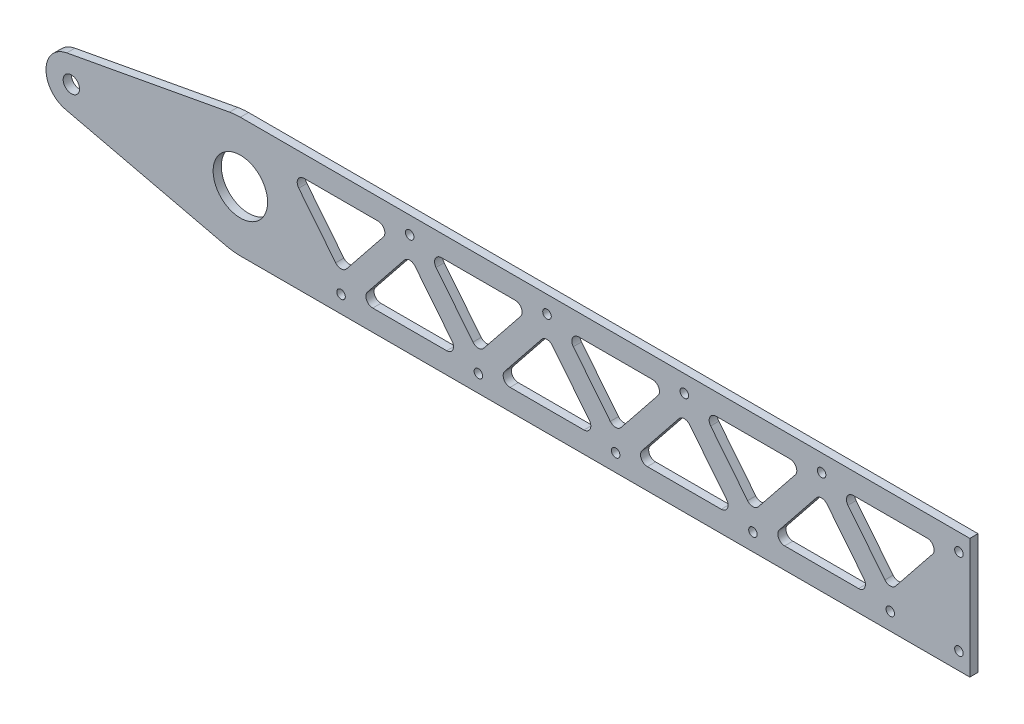
SolidWorks part; units mm, degrees
material "6061-T6 (SS)"
ref_plane "Front" through (0, 0, 0) normal (0, 0, 1) x (1, 0, 0)
ref_plane "Top" through (0, 0, 0) normal (0, 1, 0) x (1, 0, 0)
ref_plane "Right" through (0, 0, 0) normal (1, 0, 0) x (0, 0, -1)
sketch "Sketch1" plane through (0, 0, 0) normal (0, 0, 1) x (1, 0, 0)
  line L0 (-212.5, 35) -> (212.5, 35)
  line L1 (-212.5, -35) -> (212.5, -35)
  line L2 (-212.5, 0) -> (212.5, 0) construction
  line L6 (-212.5, 35) -> (-212.5, -35) construction
  line L8 (212.5, 35) -> (212.5, -35)
  line L9 (-313.6661, 16.8908) -> (-218.8625, 34.4168)
  line L10 (-314.3603, -12.0155) -> (-220.5071, -34.0718)
  arc A0 (-212.5, 35) -> (-218.8625, 34.4168) centre (-212.5, 0) ccw
  circle A2 centre (-212.5, 0) radius 15.875
  circle A4 centre (-310.9808, 2.3648) radius 4.7625
  arc A5 (-313.6661, 16.8908) -> (-314.3603, -12.0155) centre (-310.9808, 2.3648) ccw
  arc A6 (-220.5071, -34.0718) -> (-212.5, -35) centre (-212.5, 0) ccw
  point P6 (0, 0)
  dimension "D2" = 35
  dimension "D3" = 31.75
  dimension "D4" = 98.4808
  dimension "D7" = 9.525
  dimension "D6" = 14.7721
  dimension "D1" = 425
  dimension "D5" = 2.3648
extrude "Boss-Extrude1" add sketch "Sketch1" along normal blind 4.7625
sketch "Sketch6" plane through (0, 0, 0) normal (0, 0, -1) x (-1, 0, 0)
  line L0 (-166.15, 35) -> (-166.15, -35) construction
  line L1 (212.5, 35) -> (-212.5, 35) construction
  line L2 (212.5, -35) -> (-212.5, -35) construction
  line L3 (-212.5, 35) -> (-212.5, -35) construction
  circle A0 centre (212.5, 0) radius 50 construction
  dimension "D2" = 100
  dimension "D1" = 46.35
hole_wizard "#10 Clearance Hole1" positions "Sketch4" profile "Sketch5" hole size "#10" standard "ANSI Inch" end condition through all
sketch "Sketch4" plane through (0, 0, 0) normal (0, 0, -1) x (-1, 0, 0)
  line L0 (212.5, 35) -> (-212.5, 35) construction
  line L1 (212.5, -35) -> (-212.5, -35) construction
  line L2 (-166.15, 35) -> (-166.15, -35) construction
  point P4 (-126.15, 25)
  point P6 (-86.15, -25)
  dimension "D1" = 10
  dimension "D2" = 10
  dimension "D3" = 40
  dimension "D4" = 40
sketch "Sketch5" plane through (126.15, 25, 0) normal (1, 0, 0) x (0, 1, 0)
  line L0 (0, 0) -> (0, 4.7625)
  line L1 (0, 4.7625) -> (2.4892, 4.7625)
  line L2 (2.4892, 4.7625) -> (2.4892, 0)
  line L5 (2.4892, 0) -> (0, 0)
  line L11 (0, -6.35) -> (0, 107.95) construction
  dimension "Thru Hole Dia." = 4.9784
  dimension "Thru Hole Depth" = 4.7625
sketch "Sketch7" plane through (0, 0, 0) normal (0, 0, -1) x (-1, 0, 0)
pattern_linear "LPattern1" count 4 spacing 80 along (-1, 0, 0) of "#10 Clearance Hole1"
sketch "Sketch13" plane through (0, 0, 0) normal (0, 0, -1) x (-1, 0, 0)
  line L6 (-46.15, 25) -> (-86.15, -25) construction
  line L7 (-126.15, 25) -> (-86.15, -25) construction
  line L8 (-86.15, -14.5949) -> (-115.9987, 22.716)
  line L9 (-115.9987, 22.716) -> (-56.3013, 22.716)
  line L10 (-56.3013, 22.716) -> (-86.15, -14.5949)
  line L11 (-75.9987, -22.716) -> (-46.15, 14.5949)
  line L12 (-46.15, 14.5949) -> (-16.3013, -22.716)
  line L13 (-16.3013, -22.716) -> (-75.9987, -22.716)
  line L14 (-46.15, 25) -> (-6.15, -25) construction
  line L15 (-56.3013, 22.716) -> (-46.15, 14.5949) construction
  line L16 (-46.15, 14.5949) -> (-35.9987, 22.716) construction
  line L17 (-86.15, -14.5949) -> (-96.3013, -22.716) construction
  circle A0 centre (-6.15, -25) radius 2.4892 construction
  circle A1 centre (-46.15, 25) radius 2.4892 construction
  circle A2 centre (-86.15, -25) radius 2.4892 construction
  circle A3 centre (-126.15, 25) radius 2.4892 construction
  circle A4 centre (-6.15, -25) radius 2.4892
  circle A5 centre (-46.15, 25) radius 2.4892
  circle A6 centre (-86.15, -25) radius 2.4892
  circle A7 centre (-126.15, 25) radius 2.4892
  point P18 (-51.2256, 18.6554)
  point P19 (-41.0744, 18.6554)
  point P20 (-91.2256, -18.6554)
  dimension "D1" = 13
extrude "Cut-Extrude1" cut sketch "Sketch13" against normal blind 10 contours L10 L9 L8
fillet "Fillet1" radius 4 3 edges at (86.15, -14.5949, 2.3813) (56.3013, 22.716, 2.3813) (115.9987, 22.716, 2.3813)
sketch "Sketch14" plane through (0, 0, 0) normal (0, 0, -1) x (-1, 0, 0)
  line L1 (-61.5003, 16.2172) -> (-83.0265, -10.6906) construction
  line L2 (-56.3013, 22.716) -> (-86.15, -14.5949) construction
  line L3 (-46.15, 25) -> (-86.15, -25) construction
  line L4 (-46.15, 14.5949) -> (-75.9987, -22.716)
  line L5 (-75.9987, -22.716) -> (-16.3013, -22.716)
  line L6 (-16.3013, -22.716) -> (-46.15, 14.5949)
  line L7 (-89.2735, -10.6906) -> (-110.7997, 16.2172) construction
  line L8 (-86.15, -14.5949) -> (-110.7997, 16.2172) construction
  line L9 (-56.3013, 22.716) -> (-46.15, 14.5949) construction
  line L10 (-107.6762, 22.716) -> (-64.6238, 22.716) construction
  line L11 (-107.6762, 22.716) -> (-56.3013, 22.716) construction
  circle A0 centre (-6.15, -25) radius 2.4892 construction
  circle A1 centre (-86.15, -25) radius 2.4892 construction
  circle A2 centre (-46.15, 25) radius 2.4892 construction
  circle A3 centre (-6.15, -25) radius 2.4892
  circle A4 centre (-86.15, -25) radius 2.4892
  circle A5 centre (-46.15, 25) radius 2.4892
  point P16 (-51.2256, 18.6554)
extrude "Cut-Extrude2" cut sketch "Sketch14" against normal through all contours L4 L5 L6
fillet "Fillet2" radius 4 3 edges at (75.9987, -22.716, 2.3813) (16.3013, -22.716, 2.3813) (46.15, 14.5949, 2.3813)
pattern_linear "LPattern2" count 4 spacing 80 along (-1, 0, 0) of "Cut-Extrude1", "Fillet1"
pattern_linear "LPattern3" count 3 spacing 80 along (-1, 0, 0) of "Cut-Extrude2", "Fillet2"
pattern_linear "LPattern4" count 2 spacing 80 along (1, 0, 0) of "Cut-Extrude2", "Fillet2"
pattern_linear "LPattern5" count 2 spacing 80 along (1, 0, 0) of "Cut-Extrude1", "Fillet1"
sketch "Sketch15" plane through (0, 0, 4.7625) normal (0, 0, 1) x (1, 0, 0)
  line L0 (126.15, 25) -> (206.15, 25) construction
  line L1 (206.15, 25) -> (166.15, -25) construction
  line L2 (166.15, -25) -> (86.15, -25) construction
  line L3 (166.15, 35) -> (166.15, -35) construction
  line L4 (206.15, 25) -> (206.15, -25) construction
  point P3 (206.15, -25)
  point P7 (166.15, -25)
  point P13 (206.15, 25)
hole_wizard "#10 Clearance Hole2" positions "Sketch16" profile "Sketch17" hole size "#10" standard "ANSI Inch" end condition up to next
sketch "Sketch16" plane through (0, 0, 4.7625) normal (0, 0, 1) x (1, 0, 0)
  point P0 (206.15, 25)
  point P3 (206.15, -25)
  point P6 (166.15, -25)
sketch "Sketch17" plane through (206.15, 25, 4.7625) normal (1, 0, 0) x (0, -1, 0)
  line L0 (0, 0) -> (0, 4.7625)
  line L1 (0, 4.7625) -> (2.4892, 4.7625)
  line L2 (2.4892, 4.7625) -> (2.4892, 0)
  line L5 (2.4892, 0) -> (0, 0)
  line L11 (0, -6.35) -> (0, 107.95) construction
  dimension "Thru Hole Dia." = 4.9784
  dimension "Thru Hole Depth" = 4.7625
hole_wizard "CBORE for #10 Button Head Cap Screw1" positions "Sketch18" profile "Sketch21" counterbore size "#10" standard "ANSI Inch"
sketch "Sketch18" plane through (0, 0, 0) normal (0, 0, -1) x (-1, 0, 0)
  point P13 (153.85, -25)
  point P16 (73.85, -25)
sketch "Sketch21" plane through (-153.85, -25, 0) normal (1, 0, 0) x (0, 1, 0)
  line L0 (0, 0) -> (0, 4.7625)
  line L1 (0, 4.7625) -> (2.4892, 4.7625)
  line L3 (2.4892, 4.7625) -> (2.4892, 1.5875)
  line L4 (2.4892, 1.5875) -> (3.175, 1.5875)
  line L5 (3.175, 1.5875) -> (3.175, 0)
  line L7 (3.175, 0) -> (0, 0)
  line L11 (0, -6.35) -> (0, 107.95) construction
  dimension "Thru Hole Dia." = 4.9784
  dimension "Thru Hole Depth" = 4.7625
  dimension "C'Bore Dia." = 6.35
  dimension "C'Bore Depth" = 1.5875
